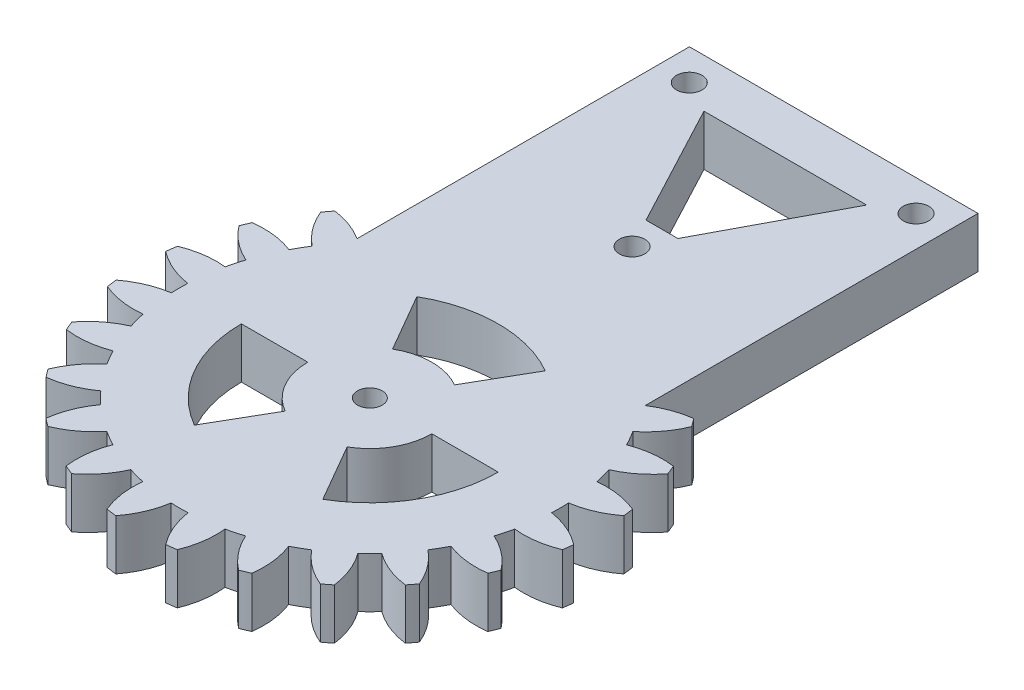
SolidWorks part; units mm, degrees
ref_plane "Front Plane" through (0, 0, 0) normal (0, 0, 1) x (1, 0, 0)
ref_plane "Top Plane" through (0, 0, 0) normal (0, 1, 0) x (1, 0, 0)
ref_plane "Right Plane" through (0, 0, 0) normal (1, 0, 0) x (0, 0, -1)
sketch "Sketch1" plane through (0, 0, 0) normal (0, 1, 0) x (1, 0, 0)
  line L1 (-16.2947, -55.4739) -> (16.2826, -55.4739)
  line L2 (-16.2947, -92.9976) -> (-16.2947, -55.4739)
  line L3 (3.5013, -113.9088) -> (7.2508, -120.4032)
  line L4 (16.2826, -93.0436) -> (16.2826, -55.4739)
  line L7 (-9.2395, -62.491) -> (-9.2962, -62.491)
  line L8 (-9.18, -60.9458) -> (9.18, -60.9458)
  line L9 (9.18, -60.9458) -> (1.8, -74.8677)
  line L10 (-9.18, -60.9458) -> (-1.8, -74.8677)
  line L11 (-1.8, -74.8677) -> (1.8, -74.8677)
  line L15 (-3.4987, -113.9088) -> (-7.2482, -120.4032)
  line L16 (-9.2962, -62.491) -> (-9.2395, -62.491)
  line L17 (-6.9987, -107.8467) -> (-14.4977, -107.8467)
  line L20 (7.0013, -107.8467) -> (14.5003, -107.8467)
  line L22 (3.5013, -101.7845) -> (7.2502, -95.2898)
  line L23 (-3.4987, -101.7845) -> (-7.2482, -95.2902)
  circle A0 centre (0, -78.2429) radius 1.44
  circle A1 centre (-12.8, -58.9858) radius 1.44
  circle A2 centre (12.8, -58.9858) radius 1.44
  arc A3 (-6.9987, -107.8467) -> (-3.4987, -113.9088) centre (0.0013, -107.8467) ccw
  arc A4 (-14.4977, -107.8467) -> (-7.2482, -120.4032) centre (0.0013, -107.8467) ccw
  arc A5 (3.5013, -113.9088) -> (7.0013, -107.8467) centre (0.0013, -107.8467) ccw
  arc A6 (7.2508, -120.4032) -> (14.5003, -107.8467) centre (0.0013, -107.8467) ccw
  arc A7 (3.5034, -101.7857) -> (-3.4987, -101.7845) centre (0.0013, -107.8467) ccw
  arc A8 (-14.4977, -107.8467) -> (-7.2482, -120.4032) centre (0.0013, -107.8467) ccw
  arc A9 (7.2502, -95.2898) -> (-7.2482, -95.2902) centre (0.0013, -107.8467) ccw
  arc A10 (7.2508, -120.4032) -> (14.5003, -107.8467) centre (0.0013, -107.8467) ccw
  arc A19 (-16.2947, -92.9976) -> (-20.2497, -91.5435) centre (-21.5044, -101.0611) ccw
  arc A20 (-20.2497, -91.5435) -> (-20.9448, -92.4467) centre (0.0013, -107.8467) ccw
  arc A21 (-20.9448, -92.4467) -> (-18.105, -96.2587) centre (-12.0659, -88.7962) ccw
  arc A22 (-18.105, -96.2587) -> (-19.061, -97.9094) centre (0.0013, -107.8467) ccw
  arc A23 (-19.061, -97.9094) -> (-23.7806, -97.3436) centre (-22.5279, -106.8615) ccw
  arc A24 (-23.7806, -97.3436) -> (-24.2194, -98.3993) centre (0.0013, -107.8467) ccw
  arc A25 (-24.2194, -98.3993) -> (-20.489, -101.3454) centre (-16.5896, -92.5731) ccw
  arc A26 (-20.489, -101.3454) -> (-20.986, -103.1932) centre (0.0013, -107.8467) ccw
  arc A27 (-20.986, -103.1932) -> (-25.6909, -103.8708) centre (-22.0125, -112.7381) ccw
  arc A28 (-25.6909, -103.8708) -> (-25.8458, -105.0497) centre (0.0013, -107.8467) ccw
  arc A29 (-25.8458, -105.0497) -> (-21.478, -106.9251) centre (-19.9922, -97.4408) ccw
  arc A30 (-21.478, -106.9251) -> (-21.478, -108.7682) centre (0.0013, -107.8467) ccw
  arc A31 (-21.478, -108.7682) -> (-25.8485, -110.6373) centre (-20.006, -118.2547) ccw
  arc A32 (-25.8485, -110.6373) -> (-25.7015, -111.7665) centre (0.0013, -107.8467) ccw
  arc A33 (-25.7015, -111.7665) -> (-20.9981, -112.4544) centre (-22.0038, -102.9073) ccw
  arc A34 (-20.9981, -112.4544) -> (-20.5075, -114.2962) centre (0.0013, -107.8467) ccw
  arc A35 (-20.5075, -114.2962) -> (-24.2454, -117.2327) centre (-16.6304, -123.0784) ccw
  arc A36 (-24.2454, -117.2327) -> (-23.8111, -118.2856) centre (0.0013, -107.8467) ccw
  arc A37 (-23.8111, -118.2856) -> (-19.0899, -117.7327) centre (-22.5324, -108.7712) ccw
  arc A38 (-19.0899, -117.7327) -> (-18.1391, -119.3849) centre (0.0013, -107.8467) ccw
  arc A39 (-18.1391, -119.3849) -> (-20.9895, -123.189) centre (-12.121, -126.8643) ccw
  arc A40 (-20.9895, -123.189) -> (-20.297, -124.0941) centre (0.0013, -107.8467) ccw
  arc A41 (-20.297, -124.0941) -> (-15.8799, -122.3378) centre (-21.5249, -114.5729) ccw
  arc A42 (-15.8799, -122.3378) -> (-14.5331, -123.6883) centre (0.0013, -107.8467) ccw
  arc A43 (-14.5331, -123.6883) -> (-16.3014, -128.1006) centre (-6.7836, -129.3545) ccw
  arc A44 (-16.3014, -128.1006) -> (-15.396, -128.7972) centre (0.0013, -107.8467) ccw
  arc A45 (-15.396, -128.7972) -> (-11.5845, -125.9568) centre (-19.0481, -119.919) ccw
  arc A46 (-11.5845, -125.9568) -> (-9.93, -126.9143) centre (0.0013, -107.8467) ccw
  arc A47 (-9.93, -126.9143) -> (-10.4941, -131.6342) centre (-0.9767, -130.3781) ccw
  arc A48 (-10.4941, -131.6342) -> (-9.4294, -132.076) centre (0.0013, -107.8467) ccw
  arc A49 (-9.4294, -132.076) -> (-6.486, -128.3436) centre (-15.2611, -124.4503) ccw
  arc A50 (-6.486, -128.3436) -> (-4.6452, -128.8375) centre (0.0013, -107.8467) ccw
  arc A51 (-4.6452, -128.8375) -> (-3.9798, -133.5401) centre (4.8974, -129.8856) ccw
  arc A52 (-3.9798, -133.5401) -> (-2.8271, -133.6924) centre (0.0013, -107.8467) ccw
  arc A53 (-2.8271, -133.6924) -> (-0.9516, -129.3245) centre (-10.436, -127.8388) ccw
  arc A54 (-0.9516, -129.3245) -> (0.9542, -129.3245) centre (0.0013, -107.8467) ccw
  arc A55 (0.9542, -129.3245) -> (2.8058, -133.695) centre (10.4451, -127.8812) ccw
  arc A56 (2.8058, -133.695) -> (3.9587, -133.5437) centre (0.0013, -107.8467) ccw
  arc A57 (3.9587, -133.5437) -> (4.6397, -128.8393) centre (-4.906, -129.8589) ccw
  arc A58 (4.6397, -128.8393) -> (6.4806, -128.3461) centre (0.0013, -107.8467) ccw
  arc A59 (6.4806, -128.3461) -> (9.4226, -132.0797) centre (15.2572, -124.4562) ccw
  arc A60 (9.4226, -132.0797) -> (10.4747, -131.6439) centre (0.0013, -107.8467) ccw
  arc A61 (10.4747, -131.6439) -> (9.915, -126.9235) centre (0.9584, -130.379) ccw
  arc A62 (9.915, -126.9235) -> (11.5655, -125.9706) centre (0.0013, -107.8467) ccw
  arc A63 (11.5655, -125.9706) -> (15.3736, -128.8155) centre (19.0363, -119.9417) ccw
  arc A64 (15.3736, -128.8155) -> (16.277, -128.1223) centre (0.0013, -107.8467) ccw
  arc A65 (16.277, -128.1223) -> (14.5146, -123.7076) centre (6.7576, -129.3635) ccw
  arc A66 (14.5146, -123.7076) -> (15.8623, -122.36) centre (0.0013, -107.8467) ccw
  arc A67 (15.8623, -122.36) -> (20.2769, -124.1224) centre (21.5181, -114.603) ccw
  arc A68 (20.2769, -124.1224) -> (20.9701, -123.2189) centre (0.0013, -107.8467) ccw
  arc A69 (20.9701, -123.2189) -> (18.1252, -119.4109) centre (12.0963, -126.8817) ccw
  arc A70 (18.1252, -119.4109) -> (19.0781, -117.7603) centre (0.0013, -107.8467) ccw
  arc A71 (19.0781, -117.7603) -> (23.7985, -118.3201) centre (22.5336, -108.8038) ccw
  arc A72 (23.7985, -118.3201) -> (24.2343, -117.268) centre (0.0013, -107.8467) ccw
  arc A73 (24.2343, -117.268) -> (20.5007, -114.326) centre (16.6108, -123.1026) ccw
  arc A74 (20.5007, -114.326) -> (20.994, -112.4851) centre (0.0013, -107.8467) ccw
  arc A75 (20.994, -112.4851) -> (25.6984, -111.804) centre (22.0135, -102.9394) ccw
  arc A76 (25.6984, -111.804) -> (25.847, -110.675) centre (0.0013, -107.8467) ccw
  arc A77 (25.847, -110.675) -> (21.4792, -108.7996) centre (19.9934, -118.2839) ccw
  arc A78 (21.4792, -108.7996) -> (21.4792, -106.8937) centre (0.0013, -107.8467) ccw
  arc A79 (21.4792, -106.8937) -> (25.847, -105.0183) centre (19.9934, -97.4094) ccw
  arc A80 (25.847, -105.0183) -> (25.6984, -103.8893) centre (0.0013, -107.8467) ccw
  arc A81 (25.6984, -103.8893) -> (20.994, -103.2082) centre (22.0135, -112.7539) ccw
  arc A82 (20.994, -103.2082) -> (20.5007, -101.3673) centre (0.0013, -107.8467) ccw
  arc A83 (20.5007, -101.3673) -> (24.2343, -98.4253) centre (16.6108, -92.5907) ccw
  arc A84 (24.2343, -98.4253) -> (23.7985, -97.3732) centre (0.0013, -107.8467) ccw
  arc A85 (23.7985, -97.3732) -> (19.0781, -97.933) centre (22.5336, -106.8895) ccw
  arc A86 (19.0781, -97.933) -> (18.1252, -96.2825) centre (0.0013, -107.8467) ccw
  arc A87 (18.1252, -96.2825) -> (20.9701, -92.4744) centre (12.0963, -88.8117) ccw
  arc A88 (20.9701, -92.4744) -> (20.2769, -91.5709) centre (0.0013, -107.8467) ccw
  arc A89 (20.2769, -91.5709) -> (16.2826, -93.0436) centre (21.5181, -101.0904) ccw
  circle A97 centre (0.0013, -107.8467) radius 1.4
  dimension "D3" = 3.3752
  dimension "D2" = 1.96
  dimension "D1" = 14
  dimension "D4" = 3.62
  dimension "D5" = 3.62
  dimension "D6" = 1.8
  dimension "D7" = 1.8
extrude "Boss-Extrude2" add sketch "Sketch1" along normal blind 5.7 contours A88 A89 L4 L1 L2 A19 A20 A21 A22 A23 A24 A25 A26 A27 A28 A29 A30 A31 A32 A33 A34 A35 A36 A37 A38 A39 A40 A41 A42 A43 A44 A45 A46 A47 A48 A49 A50 A51 A52 A53 A54 A55 A56 A57 A58 A59 A60 A61 A62 A63 A64
